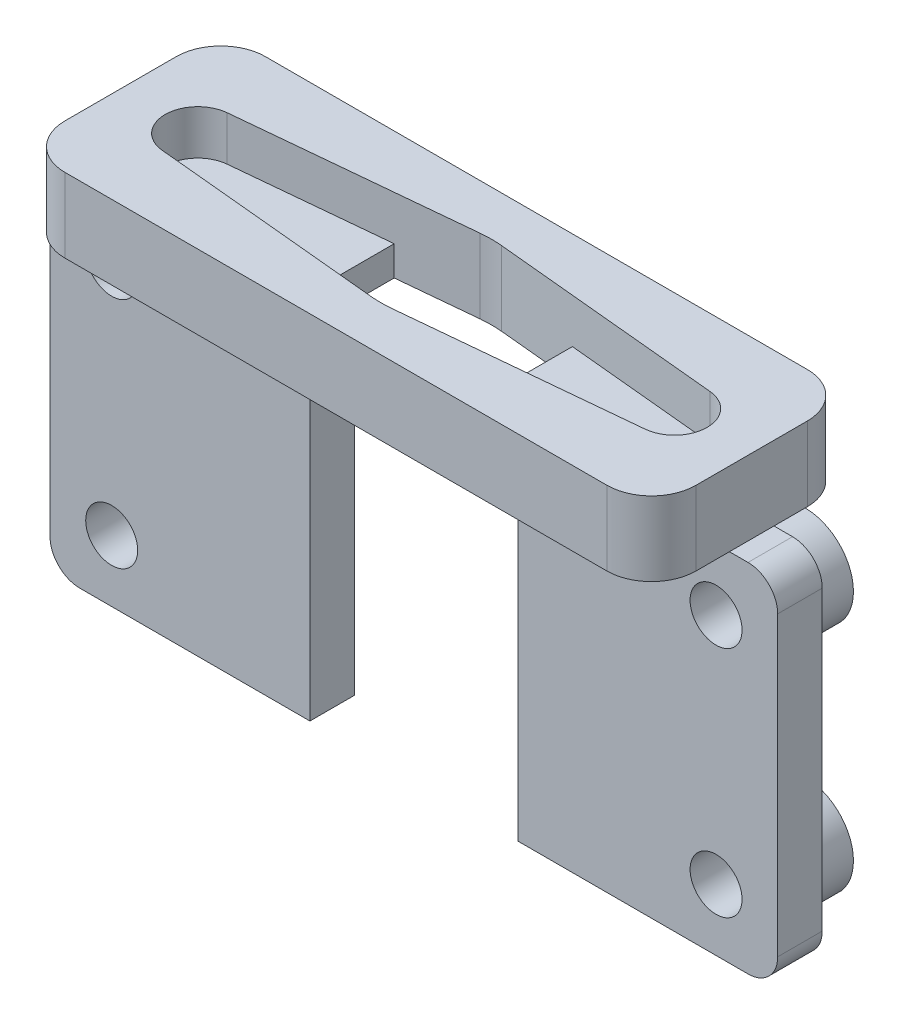
SolidWorks part; units mm, degrees
ref_plane "Front Plane" through (0, 0, 0) normal (0, 0, 1) x (1, 0, 0)
ref_plane "Top Plane" through (0, 0, 0) normal (0, 1, 0) x (1, 0, 0)
ref_plane "Right Plane" through (0, 0, 0) normal (1, 0, 0) x (0, 0, -1)
sketch "Sketch1" plane through (0, 0, 0) normal (0, 1, 0) x (1, 0, 0)
  line L0 (-18.25, 0) -> (18.25, 0) construction
  line L1 (-18.25, -3.75) -> (18.25, -3.75) construction
  line L2 (-18.25, -3.75) -> (-18.25, 3.75) construction
  line L3 (-18.25, 3.75) -> (18.25, 3.75) construction
  line L4 (18.25, -3.75) -> (18.25, 3.75) construction
  line L5 (-18.25, -3.75) -> (18.25, 3.75) construction
  line L6 (-18.25, 3.75) -> (18.25, -3.75) construction
  line L7 (-18.25, 6.75) -> (18.25, 6.75)
  line L8 (-21.25, 3.75) -> (-21.25, -3.75)
  line L9 (-18.25, -6.75) -> (18.25, -6.75)
  line L10 (21.25, 3.75) -> (21.25, -3.75)
  line L11 (-21.25, 6.75) -> (21.25, -6.75) construction
  line L12 (-21.25, -6.75) -> (21.25, 6.75) construction
  line L13 (16.2601, 2.1899) -> (0.7163, 3.6813)
  line L14 (16.2601, -2.1899) -> (0.7163, -3.6813)
  line L15 (0, -3.75) -> (0, 0) construction
  line L16 (-16.2601, -2.1899) -> (-0.7163, -3.6813)
  line L17 (-16.2601, 2.1899) -> (-0.7163, 3.6813)
  arc A0 (-18.25, 6.75) -> (-21.25, 3.75) centre (-18.25, 3.75) ccw
  arc A1 (-21.25, -3.75) -> (-18.25, -6.75) centre (-18.25, -3.75) ccw
  arc A2 (21.25, -3.75) -> (18.25, -6.75) centre (18.25, -3.75) cw
  arc A3 (21.25, 3.75) -> (18.25, 6.75) centre (18.25, 3.75) ccw
  arc A4 (16.2601, -2.1899) -> (16.2601, 2.1899) centre (16.05, 0) ccw
  arc A5 (-16.2601, -2.1899) -> (-16.2601, 2.1899) centre (-16.05, 0) cw
  arc A6 (0.7163, -3.6813) -> (-0.7163, -3.6813) centre (0, 3.7844) cw
  arc A7 (0.7163, 3.6813) -> (-0.7163, 3.6813) centre (0, -3.7844) ccw
  point P0 (0, 0)
  point P6 (0, 0)
  point P39 (0, 3.75)
  dimension "D5" = 3
  dimension "D8" = 7.5
  dimension "D1" = 36.5
  dimension "D2" = 7.5
  dimension "D3" = 3
  dimension "D4" = 3
  dimension "D6" = 2.2
  dimension "D7" = 3.75
extrude "Boss-Extrude1" add sketch "Sketch1" along normal blind 5
sketch "Sketch2" plane through (0, 0, 0) normal (0, -1, 0) x (1, 0, 0)
  line L0 (-16.2601, 2.1899) -> (-6, 3.1743)
  line L1 (-16.2601, -2.1899) -> (-6, -3.1743)
  line L2 (6, -3.1743) -> (16.2601, -2.1899)
  line L3 (16.2601, 2.1899) -> (6, 3.1743)
  line L4 (6, 3.1743) -> (6, -3.1743)
  line L5 (-6, 3.1743) -> (-6, -3.1743)
  line L6 (16.2601, -2.1899) -> (0.7163, -3.6813) construction
  arc A0 (-0.7163, 3.6813) -> (0.7163, 3.6813) centre (0, -3.7844) cw construction
  arc A1 (0.7163, -3.6813) -> (-0.7163, -3.6813) centre (0, 3.7844) cw construction
  arc A2 (-16.2601, 2.1899) -> (-16.2601, -2.1899) centre (-16.05, 0) ccw
  arc A3 (16.2601, -2.1899) -> (16.2601, 2.1899) centre (16.05, 0) ccw
  dimension "D1" = 6
  dimension "D2" = 12
extrude "Boss-Extrude2" add sketch "Sketch2" against normal blind 2
ref_plane "Plane2" through (24.5, 0, 0) normal (1, 0, 0) x (0, 0, -1)
sketch "Sketch4" plane through (24.5, 24.5, 0) normal (-1, 0, 0) x (0, -1, 0)
  line L1 (48.5, 1.5) -> (24.5, 1.5)
  line L2 (48.5, 1.5) -> (48.5, -1.5)
  line L3 (48.5, -1.5) -> (24.5, -1.5)
  line L4 (24.5, 1.5) -> (24.5, -1.5)
  line L5 (48.5, 1.5) -> (24.5, -1.5) construction
  line L6 (48.5, -1.5) -> (24.5, 1.5) construction
  line L7 (24.5, -6.75) -> (24.5, -3.75) construction
  line L8 (19.5, -3.75) -> (24.5, -3.75) construction
  point P0 (36.5, 0)
  dimension "D1" = 3
  dimension "D2" = 24
  dimension "D3" = 2.25
extrude "Boss-Extrude3" add sketch "Sketch4" along normal blind 49
sketch "Sketch5" plane through (0, 0, -1.5) normal (0, 0, -1) x (-1, 0, 0)
  line L0 (24.5, 0) -> (24.5, -24) construction
  line L1 (24.5, 0) -> (21.25, 0) construction
  line L2 (6, 0) -> (-6, 0) construction
  line L3 (7, 0) -> (-7, 0)
  line L4 (7, 0) -> (7, -24)
  line L5 (7, -24) -> (-7, -24)
  line L6 (-7, 0) -> (-7, -24)
  line L9 (24.5, -24) -> (-24.5, -24) construction
  circle A2 centre (20.35, -19.85) radius 1.75
  circle A3 centre (-20.35, -19.85) radius 1.75
  circle A4 centre (-20.35, -4.15) radius 1.75
  circle A5 centre (20.35, -4.15) radius 1.75
  dimension "D1" = 40.7
  dimension "D2" = 3.5
  dimension "D3" = 3.5
  dimension "D4" = 3.5
  dimension "D5" = 3.5
  dimension "D6" = 15.7
  dimension "D7" = 4.15
  dimension "D8" = 4.15
  dimension "D10" = 14
  dimension "D13" = 17.5
extrude "Cut-Extrude1" cut sketch "Sketch5" against normal up to next
sketch "Sketch6" plane through (0, 0, -1.5) normal (0, 0, -1) x (-1, 0, 0)
  circle A0 centre (-20.35, -4.15) radius 1.75
  circle A1 centre (20.35, -4.15) radius 1.75
  circle A2 centre (20.35, -19.85) radius 1.75
  circle A3 centre (-20.35, -19.85) radius 1.75
  circle A4 centre (-20.35, -4.15) radius 1.75 construction
  circle A5 centre (-20.35, -4.15) radius 3.25
  circle A6 centre (20.35, -4.15) radius 3.25
  circle A7 centre (20.35, -19.85) radius 3.25
  circle A8 centre (-20.35, -19.85) radius 3.25
  dimension "D1" = 1.5
extrude "Boss-Extrude4" add sketch "Sketch6" along normal blind 3
fillet "Fillet1" radius 2 4 edges at (24.5, -24, 0) (24.5, 0, 0) (-24.5, -24, 0) (-24.5, 0, 0)
